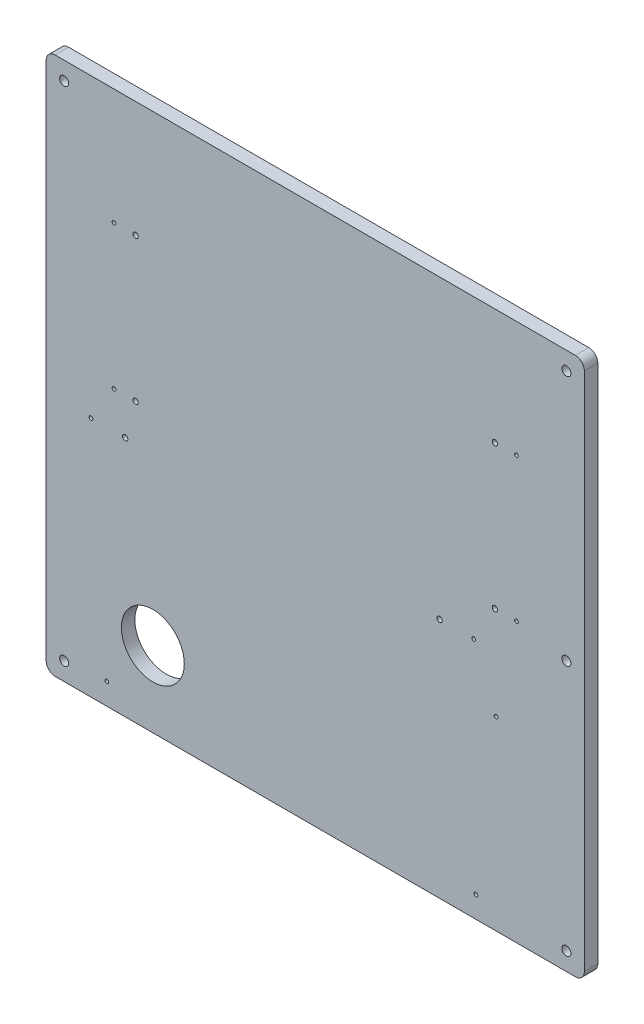
SolidWorks part; units mm, degrees
ref_plane "Front Plane" through (0, 0, 0) normal (0, 0, 1) x (1, 0, 0)
ref_plane "Top Plane" through (0, 0, 0) normal (0, 1, 0) x (1, 0, 0)
ref_plane "Right Plane" through (0, 0, 0) normal (1, 0, 0) x (0, 0, -1)
sketch "Sketch1" plane through (0, 0, 0) normal (0, 0, 1) x (1, 0, 0)
  line L1 (-299.5, -299.5) -> (299.5, -299.5)
  line L2 (-299.5, -299.5) -> (-299.5, 299.5)
  line L3 (-299.5, 299.5) -> (299.5, 299.5)
  line L4 (299.5, -299.5) -> (299.5, 299.5)
  line L5 (-299.5, -299.5) -> (299.5, 299.5) construction
  line L6 (-299.5, 299.5) -> (299.5, -299.5) construction
  point P0 (0, 0)
  dimension "D1" = 599
  dimension "D2" = 599
extrude "Boss-Extrude1" add sketch "Sketch1" along normal blind 15
sketch "Sketch2" plane through (0, 0, 15) normal (0, 0, 1) x (1, 0, 0)
  line L0 (-299.5, -299.5) -> (299.5, -299.5) construction
  line L1 (-299.5, 299.5) -> (-299.5, -299.5) construction
  line L2 (299.5, -299.5) -> (299.5, 299.5) construction
  line L3 (299.5, 299.5) -> (-299.5, 299.5) construction
  circle A0 centre (-279.5, -279.5) radius 5
  circle A1 centre (279.5, -279.5) radius 5
  circle A2 centre (-279.5, 279.5) radius 5
  circle A3 centre (279.5, 279.5) radius 5
  circle A5 centre (279.5, 0) radius 5
  dimension "D1" = 10
  dimension "D2" = 20
  dimension "D3" = 20
  dimension "D4" = 20
  dimension "D5" = 20
extrude "Cut-Extrude1" cut sketch "Sketch2" against normal through all
fillet "Fillet1" radius 10
sketch "Sketch3" plane through (0, 0, 15) normal (0, 0, 1) x (1, 0, 0)
  line L2 (-299.5, 289.5) -> (-299.5, -289.5) construction
  line L3 (-289.5, -299.5) -> (289.5, -299.5) construction
  circle A0 centre (-180.79, -215.5) radius 35
  dimension "D1" = 70
  dimension "D2" = 118.71
  dimension "D3" = 84
extrude "Cut-Extrude2" cut sketch "Sketch3" against normal through all
sketch "Sketch4" plane through (0, 0, 15) normal (0, 0, 1) x (1, 0, 0)
  circle A0 centre (-200, 170.5) radius 3
  circle A1 centre (-200, 10.5) radius 3
  circle A2 centre (200, 170.5) radius 3
  circle A3 centre (200, 10.5) radius 3
  circle A4 centre (138.4, -30.5) radius 3
  circle A5 centre (-211.6, -30.5) radius 3
  dimension "D1" = 6
extrude "Cut-Extrude3" cut sketch "Sketch4" against normal through all
sketch "Sketch5" plane through (0, 0, 15) normal (0, 0, 1) x (1, 0, 0)
  circle A0 centre (-224, 170.5) radius 2.1
  circle A1 centre (224, 170.5) radius 2.1
  circle A2 centre (224, 10.5) radius 2.1
  circle A3 centre (201.2362, -92.9825) radius 2.1
  circle A4 centre (178.85, -275.5) radius 2.1
  circle A5 centre (-231.95, -275.5) radius 2.1
  circle A6 centre (-249.6, -30.5) radius 2.1
  circle A7 centre (-224, 10.5) radius 2.1
  circle A8 centre (176.4, -30.5) radius 2.1
  dimension "D1" = 4.2
extrude "Cut-Extrude4" cut sketch "Sketch5" against normal through all
sketch "Sketch6" plane through (0, 0, 0) normal (0, 0, -1) x (-1, 0, 0)
  text T0 "bovenkant" font "Century Gothic" height in points 48
